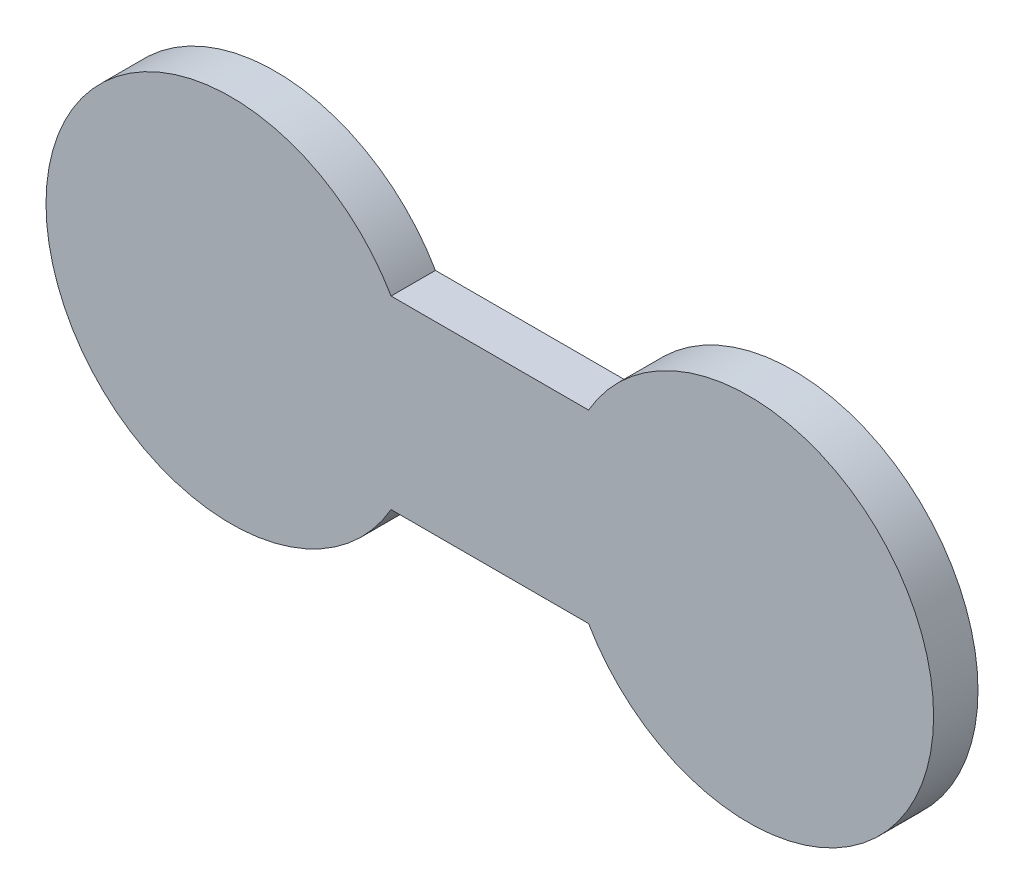
SolidWorks part; units mm, degrees
ref_plane "Plan de face" through (0, 0, 0) normal (0, 0, 1) x (1, 0, 0)
ref_plane "Plan de dessus" through (0, 0, 0) normal (0, 1, 0) x (1, 0, 0)
ref_plane "Plan de droite" through (0, 0, 0) normal (1, 0, 0) x (0, 0, -1)
sketch "Esquisse1" plane through (0, 0, 0) normal (0, 0, 1) x (1, 0, 0)
  line L1 (-30, -12.5) -> (30, -12.5)
  line L2 (-30, -12.5) -> (-30, 12.5)
  line L3 (-30, 12.5) -> (30, 12.5)
  line L4 (30, -12.5) -> (30, 12.5)
  line L5 (-30, -12.5) -> (30, 12.5) construction
  line L6 (-30, 12.5) -> (30, -12.5) construction
  point P0 (0, 0)
  dimension "D1" = 60
  dimension "D2" = 25
extrude "Boss.-Extru.2" add sketch "Esquisse1" along normal blind 3
sketch "Esquisse2" plane through (0, 0, 3) normal (0, 0, 1) x (1, 0, 0)
  line L0 (0, 6.25) -> (0, -6.25)
  line L7 (-6.6747, 6.25) -> (6.6747, 6.25)
  line L9 (-6.6747, -6.25) -> (6.6747, -6.25)
  arc A0 (-6.6747, 6.25) -> (-6.6747, -6.25) centre (-17.5, 0) ccw
  arc A1 (6.6747, 6.25) -> (6.6747, -6.25) centre (17.5, 0) cw
  point P17 (0, 6.25)
  point P22 (0, -6.25)
  point P26 (0, 0.625)
  point P29 (0, -0.625)
  line M6 (30, -12.5) -> (30, 12.5)
  line M7 (30, 12.5) -> (-30, 12.5)
  line M8 (-30, 12.5) -> (-30, -12.5)
  line M9 (-30, -12.5) -> (30, -12.5)
extrude "Enlèv. mat.-Extru.1" cut sketch "Esquisse2" against normal blind 10 contours L7 A1 A0 M7 | A0 M7 M8 | A0 M8 M9 | A1 L9 A0 M9 | A1 M6 M9 | A1 M7 M6
